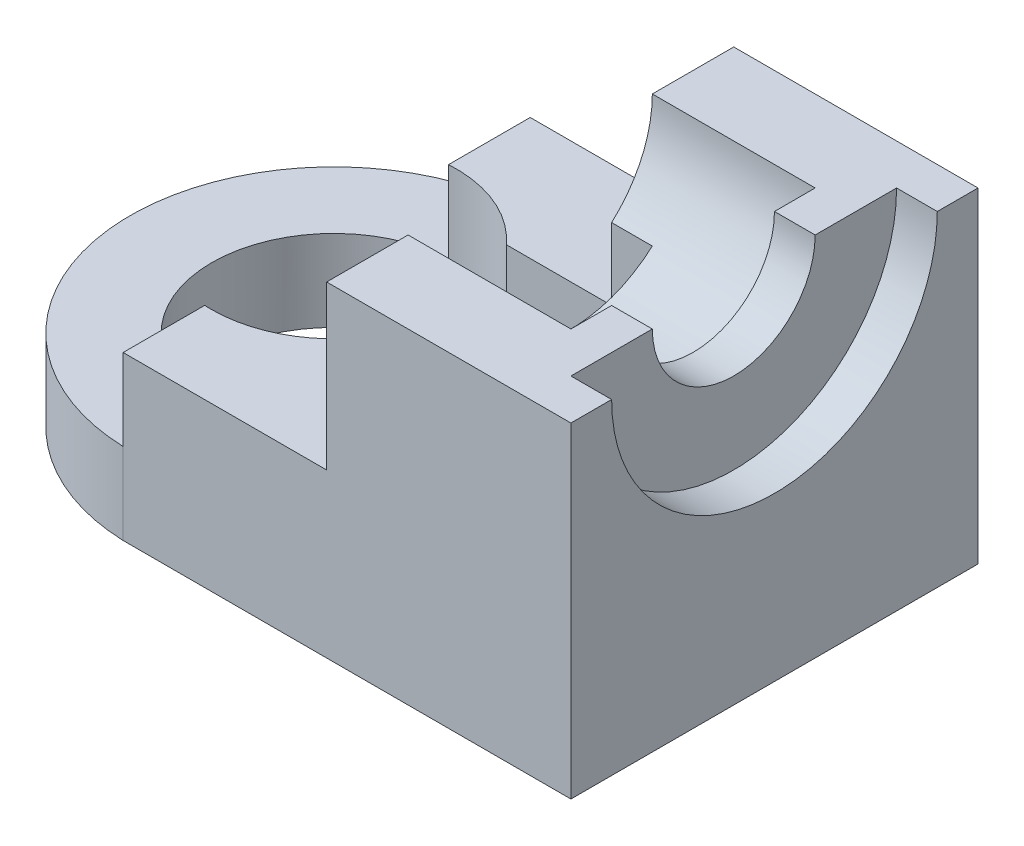
SolidWorks part; units mm, degrees
ref_plane "Front" through (0, 0, 0) normal (0, 0, 1) x (1, 0, 0)
ref_plane "Top" through (0, 0, 0) normal (0, 1, 0) x (1, 0, 0)
ref_plane "Right" through (0, 0, 0) normal (1, 0, 0) x (0, 0, -1)
sketch "Sketch1" plane through (0, 0, 0) normal (1, 0, 0) x (0, 0, -1)
  line L0 (-2, 4) -> (-5, 4)
  line L1 (5, -4) -> (-5, -4)
  line L2 (5, -4) -> (5, 4)
  line L3 (5, 4) -> (2, 4)
  line L4 (-5, -4) -> (-5, 4)
  line L5 (5, -4) -> (-5, 4) construction
  line L6 (5, 4) -> (-5, -4) construction
  arc A0 (-2, 4) -> (2, 4) centre (0, 4) ccw
  point P0 (0, 0)
  dimension "D3" = 4
  dimension "D4" = 3
  dimension "D1" = 8
  dimension "D2" = 10
  dimension "D5" = 3
extrude "Boss-Extrude1" add sketch "Sketch1" along normal blind 16
sketch "Sketch2" plane through (0, 4, 0) normal (0, 1, 0) x (1, 0, 0)
  line L0 (16, -5) -> (0, -5) construction
  line L1 (16, 5) -> (0, 5) construction
  line L2 (0, -2) -> (0, -5) construction
  line L3 (0, 5) -> (0, 2) construction
  line L4 (5, 5) -> (0, 5)
  line L5 (0, 5) -> (0, -5)
  line L6 (0, -5) -> (5, -5)
  arc A0 (5, -5) -> (5, 5) centre (5.1762, 0) cw
  circle A1 centre (5.1762, 0) radius 3
  dimension "D3" = 5.0031
  dimension "D4" = 6
  dimension "D1" = 5
  dimension "D2" = 5
extrude "Cut-Extrude1" cut sketch "Sketch2" against normal blind 18
sketch "Sketch3" plane through (16, 0, 0) normal (1, 0, 0) x (0, 0, -1)
  circle A0 centre (0, 4) radius 4
  dimension "D1" = 8
extrude "Cut-Extrude2" cut sketch "Sketch3" against normal blind 1
sketch "Sketch4" plane through (0, 0, 0) normal (1, 0, 0) x (0, 0, -1)
  circle A0 centre (0, 4) radius 3
  dimension "D1" = 6
extrude "Cut-Extrude3" cut sketch "Sketch4" along normal blind 14
sketch "Sketch5" plane through (0, 4, 0) normal (0, 1, 0) x (1, 0, 0)
  line L1 (5, 5) -> (-1.8031, 5)
  line L2 (5, 5) -> (5, -5.1022)
  line L3 (5, -5.1022) -> (-1.8031, -5.1022)
  line L4 (-1.8031, 5) -> (-1.8031, -5.1022)
extrude "Cut-Extrude4" cut sketch "Sketch5" against normal blind 6
sketch "Sketch6" plane through (0, 4, 0) normal (0, 1, 0) x (1, 0, 0)
  line L0 (16, -5) -> (5, -5) construction
  line L1 (5, 5) -> (10, 5)
  line L2 (5, 5) -> (5, -5)
  line L3 (5, -5) -> (10, -5)
  line L4 (10, 5) -> (10, -5)
  dimension "D1" = 5
extrude "Cut-Extrude5" cut sketch "Sketch6" against normal blind 4
sketch "Sketch7" plane through (0, 0, 0) normal (0, 1, 0) x (1, 0, 0)
  line L5 (11, 2) -> (4.6571, 2)
  line L6 (11, 2) -> (11, -2)
  line L7 (11, -2) -> (4.6571, -2)
  line L8 (4.6571, 2) -> (4.6571, -2)
  line L9 (10, 5) -> (5, 5) construction
  line L10 (10, -5) -> (10, 5) construction
  point P0 (0, 0)
  point P10 (0, 0)
  dimension "D1" = 4
  dimension "D2" = 3
  dimension "D3" = 1
extrude "Cut-Extrude6" cut sketch "Sketch7" against normal blind 2 and the other way blind 4
